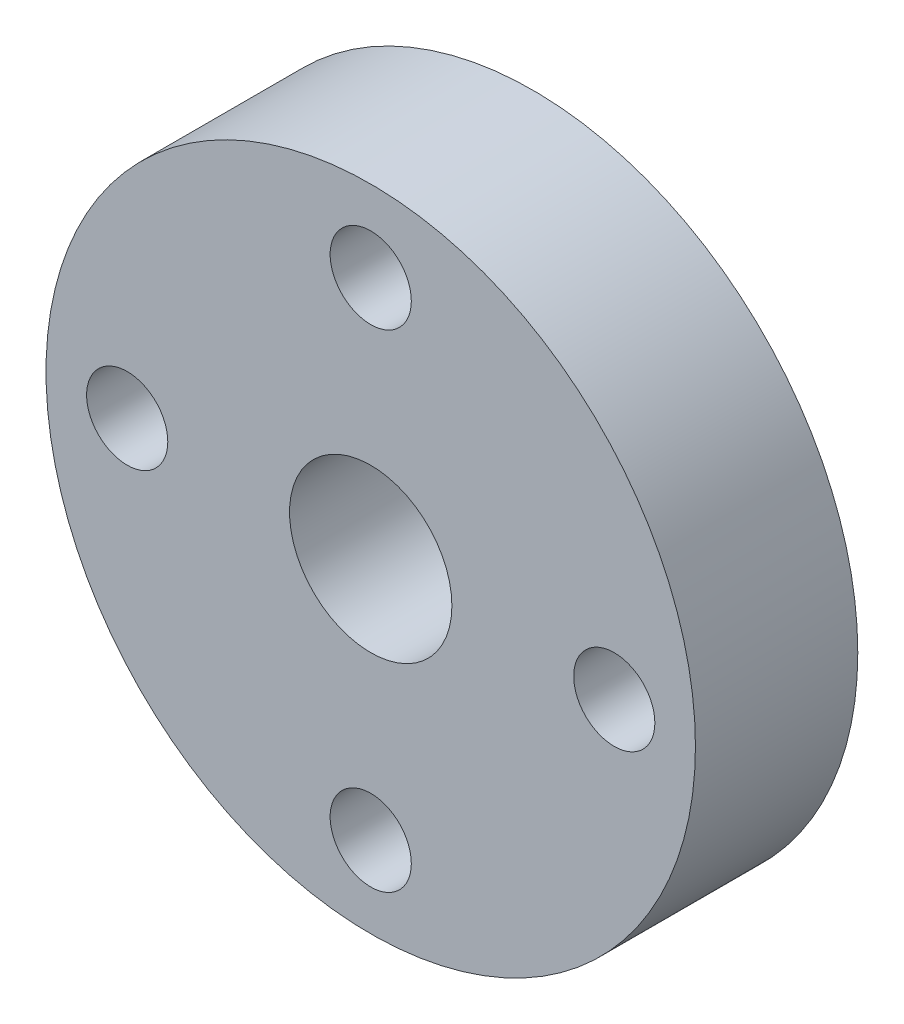
SolidWorks part; units mm, degrees
ref_plane "Front Plane" through (0, 0, 0) normal (0, 0, 1) x (1, 0, 0)
ref_plane "Top Plane" through (0, 0, 0) normal (0, 1, 0) x (1, 0, 0)
ref_plane "Right Plane" through (0, 0, 0) normal (1, 0, 0) x (0, 0, -1)
sketch "Sketch1" plane through (0, 0, 0) normal (0, 0, 1) x (1, 0, 0)
  line L0 (0, 0) -> (0, 34.2588) construction
  circle A0 centre (0, 0) radius 20
  circle A1 centre (0, 0) radius 5
  circle A2 centre (0, 15) radius 2.5
  circle A3 centre (15, 0) radius 2.5
  circle A4 centre (0, -15) radius 2.5
  circle A5 centre (-15, 0) radius 2.5
  point P16 (0, 0)
  dimension "D1" = 40
  dimension "D2" = 10
  dimension "D3" = 15
  dimension "D4" = 5
  dimension "D5" = 4
extrude "Boss-Extrude1" add sketch "Sketch1" along normal blind 10
